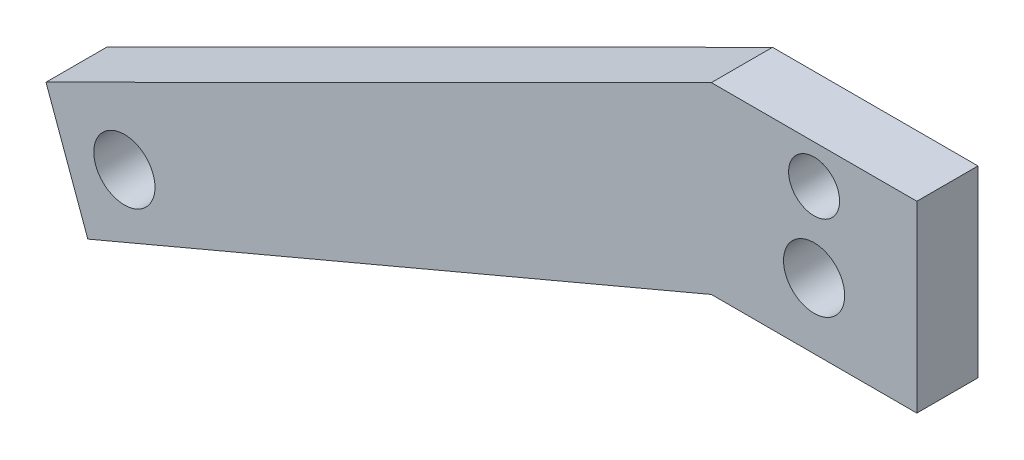
SolidWorks part; units mm, degrees
ref_plane "Front Plane" through (0, 0, 0) normal (0, 0, 1) x (1, 0, 0)
ref_plane "Top Plane" through (0, 0, 0) normal (0, 1, 0) x (1, 0, 0)
ref_plane "Right Plane" through (0, 0, 0) normal (1, 0, 0) x (0, 0, -1)
sketch "Sketch1" plane through (0, 0, 0) normal (0, 0, 1) x (1, 0, 0)
  line L0 (-16, 45) -> (-119.6152, -6.7525)
  line L2 (-276.7879, -13.7826) -> (-251.7788, -35.3348) construction
  line L3 (0, 26.6476) -> (-107.4069, -12.4453) construction
  line L4 (-16, 45) -> (-16, 15)
  line L5 (-16, 15) -> (16, 15)
  line L6 (16, 15) -> (16, 45)
  line L7 (16, 45) -> (-16, 45)
  line L8 (-16, 45) -> (-16, 16.425) construction
  line L9 (-16, 15) -> (16, 15) construction
  line L10 (16, 16.425) -> (16, 45)
  line L11 (16, 45) -> (-16, 45)
  line L12 (16, 16.425) -> (-16, 16.425)
  line L13 (-16, 16.425) -> (-113.0997, -24.6536)
  line L14 (-113.0997, -24.6536) -> (-119.6152, -6.7525)
  line L15 (-251.7788, -35.3348) -> (-242.2031, -37.4927) construction
  line L17 (-30.3277, 26.2961) -> (-28.037, 26.7) construction
  line L18 (-2117.156, -341.6) -> (-28.037, 26.7) construction
  line L19 (-242.2031, -37.4927) -> (-208.8903, -37.4927) construction
  line L20 (-208.8903, -37.4927) -> (-16, 45) construction
  line L21 (-292.5067, -43.5335) -> (-248.9466, -55.1606) construction
  line L22 (-248.9466, -55.1606) -> (-208.8903, -56.2396) construction
  line L23 (-208.8903, -56.2396) -> (-14.9476, 16.425) construction
  line L24 (-288.0555, -26.8574) -> (0, 26.6476) construction
  line L47 (-107.4069, -12.4453) -> (-116.3574, -15.7031) construction
  circle A0 centre (0, 39) radius 3.9688 construction
  circle A1 centre (0, 39) radius 3.9688
  circle A2 centre (0, 26.6476) radius 4.7625
  circle A3 centre (-107.4069, -12.4453) radius 4.7625
  circle A4 centre (-288.0555, -26.8574) radius 17.26 construction
  point P19 (0, 0)
  point P21 (-116.3574, -15.7031)
  point P22 (-37.2984, 17.3696)
  dimension "D2" = 9.525
  dimension "D4" = 114.3
  dimension "D7" = 292.9825
  dimension "D3" = 9.525
  dimension "D5" = 19.05
  dimension "D6" = 28.575
  dimension "D8" = 20
  dimension "D9" = 32
  dimension "D1" = 0
extrude "Boss-Extrude1" add sketch "Sketch1" along normal blind 9.525
